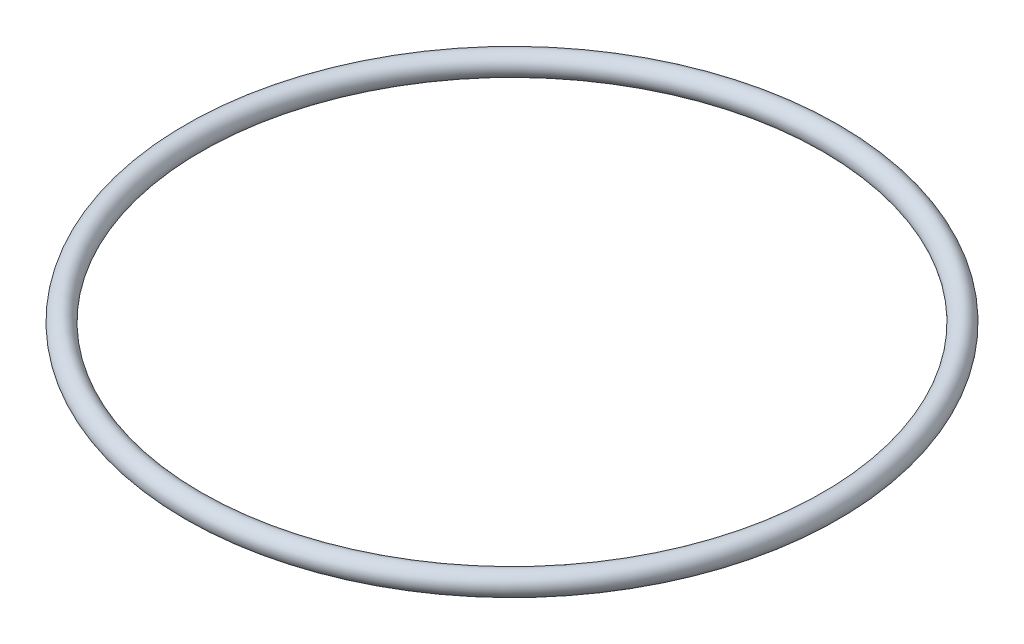
SolidWorks part; units mm, degrees
ref_plane "Front Plane" through (0, 0, 0) normal (0, 0, 1) x (1, 0, 0)
ref_plane "Top Plane" through (0, 0, 0) normal (0, 1, 0) x (1, 0, 0)
ref_plane "Right Plane" through (0, 0, 0) normal (1, 0, 0) x (0, 0, -1)
sketch "Sketch1" plane through (0, 0, 0) normal (0, 0, 1) x (1, 0, 0)
  line L0 (0, 0) -> (0, 3.8197) construction
  circle A0 centre (-29, 0) radius 1
  dimension "D1" = 2
  dimension "D2" = 29
revolve "Revolve1" add sketch "Sketch1" angle 360 about L0
sketch "Sketch2" plane through (0, 0, 0) normal (0, 1, 0) x (1, 0, 0)
  circle A0 centre (0, 0) radius 29
  dimension "D1" = 58
